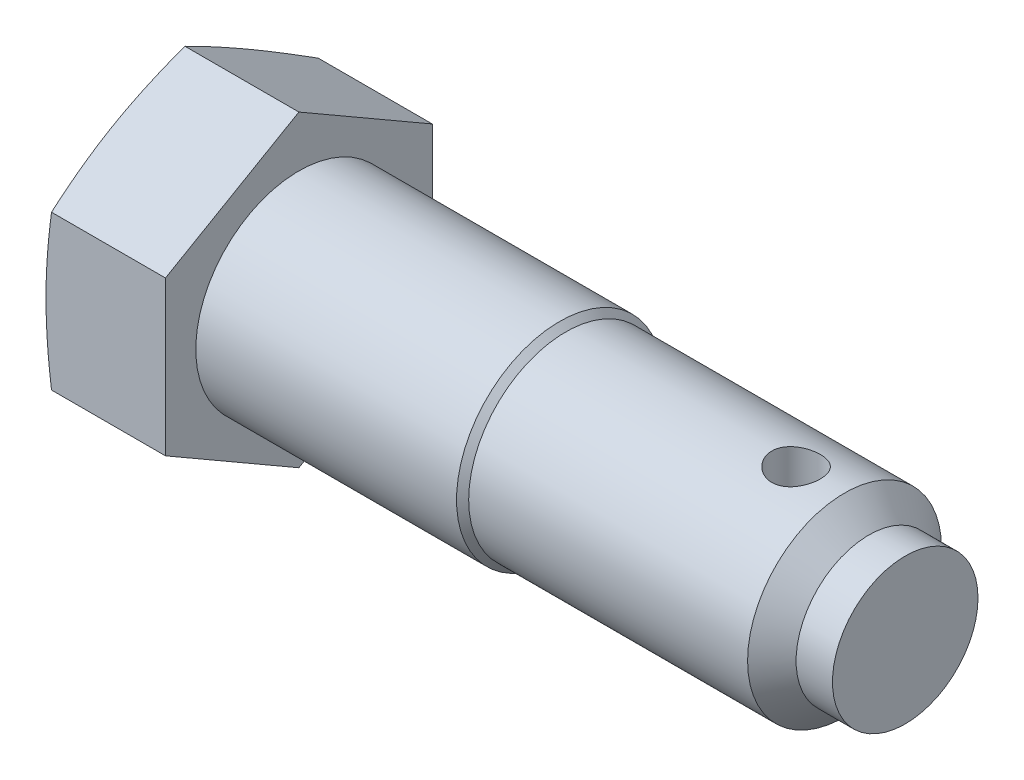
SolidWorks part; units mm, degrees
ref_plane "Плоскость1" through (0, 0, 0) normal (0, 0, 1) x (1, 0, 0)
ref_plane "Плоскость2" through (0, 0, 0) normal (0, 1, 0) x (1, 0, 0)
ref_plane "Плоскость3" through (0, 0, 0) normal (1, 0, 0) x (0, 0, -1)
sketch "BodySke" plane through (0, 0, 0) normal (0, 0, 1) x (1, 0, 0)
  line L0 (0, 0) -> (-13.929, 0) construction
  line L1 (0, 0) -> (0, 8.5)
  line L2 (0, 8.5) -> (21.5, 8.5)
  line L3 (21.5, 8.5) -> (22, 8)
  line L4 (22, 8) -> (45, 8)
  line L5 (45, 8) -> (47, 6)
  line L6 (47, 6) -> (50, 6)
  line L7 (50, 6) -> (50, 0)
  line L8 (50, 0) -> (0, 0)
  dimension "D1" = 17
  dimension "Diameter" = 16
  dimension "D2" = 12
  dimension "L2" = 22
  dimension "L3" = 3
  dimension "D7" = 45
  dimension "D8" = 45
  dimension "Length" = 50
revolve "BaseBody" add sketch "BodySke" angle 360 about L0
cosmetic thread "ThreadCosmetic" parameters "Minor_dia"=13.797
sketch "Ske" plane through (0, 0, 0) normal (-1, 0, 0) x (0, 0, 1)
  line L1 (0, 12.7017) -> (-11, 6.3509)
  line L2 (-11, 6.3509) -> (-11, -6.3509)
  line L3 (-11, -6.3509) -> (0, -12.7017)
  line L4 (0, -12.7017) -> (11, -6.3509)
  line L5 (11, -6.3509) -> (11, 6.3509)
  line L6 (11, 6.3509) -> (0, 12.7017)
  circle A0 centre (0, 0) radius 11 construction
  dimension "Width_Flats" = 22
extrude "BaseHead" add sketch "Ske" along normal blind 10
sketch "Ske1" plane through (0, 0, 0) normal (0, 0, 1) x (1, 0, 0)
  line L0 (0, 0) -> (-7.7485, 0) construction
  line L1 (0, 0) -> (-13.929, 0) construction
  line L2 (-10, 12.7017) -> (0, 12.7017) construction
  line L3 (-10, 6.3509) -> (-10, 12.7017) construction
  line L4 (-10, 12.7017) -> (-9.3967, 12.7017)
  line L5 (-10, 10.45) -> (-10, 12.7017)
  line L6 (-9.3967, 12.7017) -> (-10, 10.45)
  dimension "D1" = 20.9
  dimension "Head_ch_ang" = 15
revolve "HeadFillet" cut sketch "Ske1" angle 360 about L0
sketch "Ske2" plane through (0, 0, 0) normal (0, 1, 0) x (1, 0, 0)
  line L0 (0, -11) -> (0, 0) construction
  line L1 (-9.3967, 0) -> (0, 0) construction
  circle A0 centre (41, 0) radius 2
  dimension "D3" = 4
  dimension "LContr" = 41
extrude "Hole" cut sketch "Ske2" against normal through all and the other way through all
equation "\"D1@Ske1\" = .95 * \"Width_Flats@Ske\""
